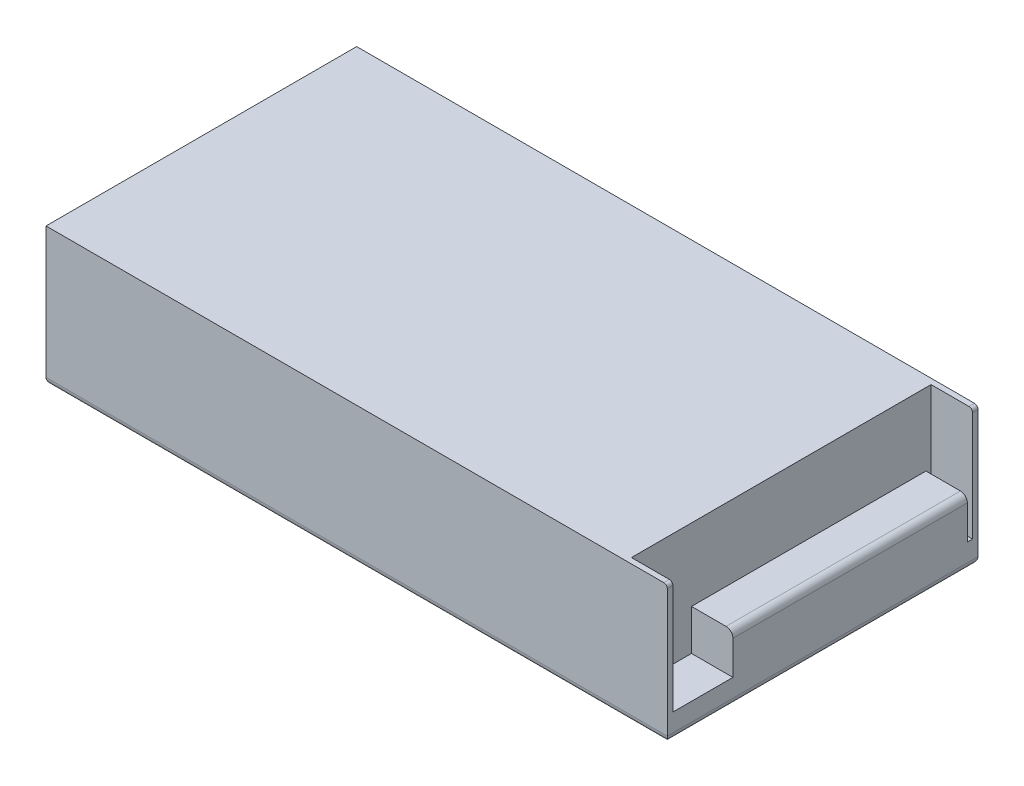
SolidWorks part; units mm, degrees
material "1060 Alloy"
ref_plane "Front Plane" through (0, 0, 0) normal (0, 0, 1) x (1, 0, 0)
ref_plane "Top Plane" through (0, 0, 0) normal (0, 1, 0) x (1, 0, 0)
ref_plane "Right Plane" through (0, 0, 0) normal (1, 0, 0) x (0, 0, -1)
sketch "Sketch1" plane through (0, 0, 0) normal (0, 1, 0) x (1, 0, 0)
  line L1 (-54.2293, 44.7122) -> (174.3707, 44.7122)
  line L2 (-54.2293, 44.7122) -> (-54.2293, -69.5878)
  line L3 (-54.2293, -69.5878) -> (174.3707, -69.5878)
  line L4 (174.3707, 44.7122) -> (174.3707, -69.5878)
  dimension "D1" = 228.6
  dimension "D2" = 114.3
extrude "Boss-Extrude1" add sketch "Sketch1" along normal blind 50.8
sketch "Sketch2" plane through (0, 50.8, 0) normal (0, 1, 0) x (1, 0, 0)
  line L1 (159.1307, 42.6802) -> (174.3707, 42.6802)
  line L2 (159.1307, 42.6802) -> (159.1307, -67.5558)
  line L3 (159.1307, -67.5558) -> (174.3707, -67.5558)
  line L4 (174.3707, 42.6802) -> (174.3707, -67.5558)
  line L6 (-54.2293, -69.5878) -> (174.3707, -69.5878) construction
  line L7 (174.3707, 44.7122) -> (-54.2293, 44.7122) construction
  line L8 (174.3707, -69.5878) -> (174.3707, 44.7122) construction
  dimension "D1" = 15.24
  dimension "D2" = 2.032
  dimension "D3" = 2.032
extrude "Cut-Extrude1" cut sketch "Sketch2" against normal blind 41.6052
sketch "Sketch3" plane through (0, 9.1948, 0) normal (0, 1, 0) x (1, 0, 0)
  line L0 (159.1307, 42.6802) -> (159.1307, -67.5558) construction
  line L1 (174.3707, -45.4578) -> (159.1307, -45.4578)
  line L2 (174.3707, -45.4578) -> (174.3707, 40.8006)
  line L3 (174.3707, 40.8006) -> (159.1307, 40.8006)
  line L4 (159.1307, -45.4578) -> (159.1307, 40.8006)
  line L5 (159.1307, -67.5558) -> (174.3707, -67.5558) construction
  line L6 (174.3707, 42.6802) -> (159.1307, 42.6802) construction
  line L9 (174.3707, -67.5558) -> (174.3707, 42.6802) construction
  dimension "D2" = 22.098
  dimension "D3" = 1.8796
extrude "Boss-Extrude2" add sketch "Sketch3" along normal blind 14.986
fillet "Fillet1" radius 2.54 1 edges at (174.3707, 24.1808, 2.3286)
fillet "Fillet2" radius 1.27 2 edges at (174.3707, 50.8, -43.6962) (174.3707, 50.8, 68.5718)
fillet "Fillet3" radius 2.54 4 edges at (-54.2293, 0, 12.4378) (174.3707, 0, 12.4378) (60.0707, 0, -44.7122) (60.0707, 0, 69.5878)
